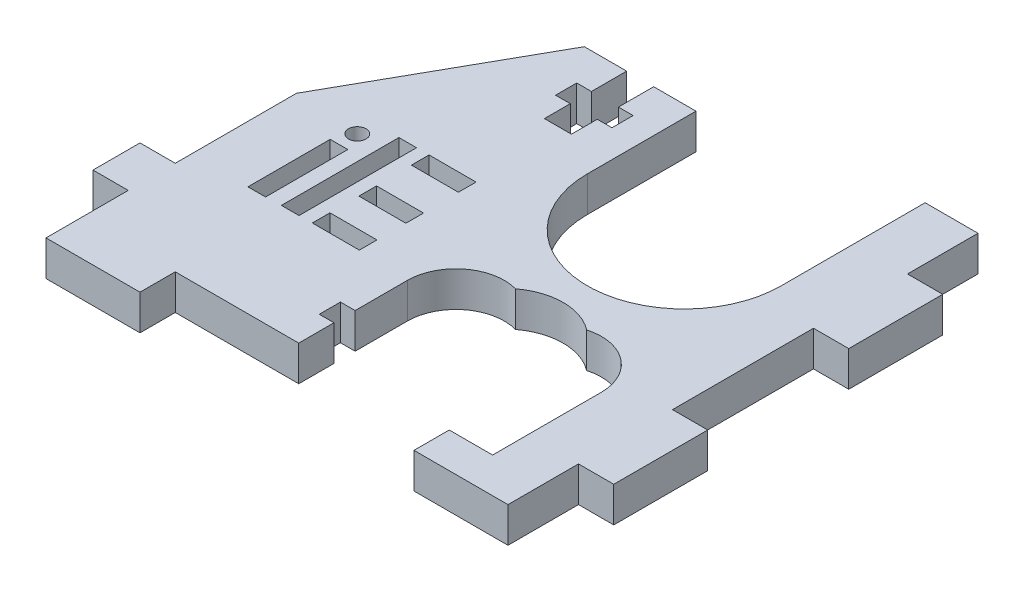
SolidWorks part; units mm, degrees
ref_plane "Front Plane" through (0, 0, 0) normal (0, 0, 1) x (1, 0, 0)
ref_plane "Top Plane" through (0, 0, 0) normal (0, 1, 0) x (1, 0, 0)
ref_plane "Right Plane" through (0, 0, 0) normal (1, 0, 0) x (0, 0, -1)
sketch "Sketch1" plane through (0, 0, 0) normal (0, 1, 0) x (1, 0, 0)
  line L1 (15.25, 17) -> (-15.25, 17)
  line L2 (15.25, 17) -> (15.25, -17)
  line L3 (15.25, -17) -> (-15.25, -17)
  line L4 (-15.25, 17) -> (-15.25, -17)
  line L5 (15.25, 17) -> (-15.25, -17) construction
  line L6 (15.25, -17) -> (-15.25, 17) construction
  point P0 (0, 0)
  dimension "D1" = 30.5
  dimension "D2" = 34
extrude "Boss-Extrude1" add sketch "Sketch1" along normal mid plane 3
sketch "Sketch2" plane through (0, 1.5, 0) normal (0, 1, 0) x (1, 0, 0)
  line L1 (-15.25, 17) -> (-24.07, 1.309)
  line L2 (-55.3828, -17) -> (-15.25, -17)
  line L3 (-15.25, -17) -> (15.25, -17) construction
  line L4 (-15.25, 17) -> (-15.25, -17)
  line L6 (-55.3828, -17) -> (-55.3828, -27.8535) construction
  spline S0 degree 3 poles (-24.07, 1.309) (-25.6121, -1.4345) (-30.226, -1.523) (-46.6978, -11.0884) (-55.3828, -10.3072) (-55.3828, -17) knots 0 0 0 0 0.22113 0.6036 1 1 1 1
  dimension "D2" = 8.82
  dimension "D1" = 18
extrude "Boss-Extrude2" add sketch "Sketch2" against normal up to vertex (3 mm away)
sketch "Sketch3" plane through (0, 1.5, 0) normal (0, 1, 0) x (1, 0, 0)
  line L0 (15.25, -17) -> (15.25, 17) construction
  line L1 (15.25, 14) -> (18.25, 14)
  line L2 (15.25, 14) -> (15.25, 6)
  line L3 (15.25, 6) -> (18.25, 6)
  line L4 (18.25, 14) -> (18.25, 6)
  line L5 (16.75, -6) -> (16.75, 6) construction
  line L6 (15.25, -6) -> (18.25, -6)
  line L7 (15.25, -6) -> (15.25, -14)
  line L8 (15.25, -14) -> (18.25, -14)
  line L9 (18.25, -6) -> (18.25, -14)
  line L10 (0, 0) -> (16.75, 0) construction
  line L11 (-55.3828, -17) -> (15.25, -17) construction
  line L12 (-15.25, 17) -> (-7.25, 17)
  line L13 (-15.25, 17) -> (-15.25, 20)
  line L14 (-15.25, 20) -> (-7.25, 20)
  line L15 (-7.25, 17) -> (-7.25, 20)
  line L16 (15.25, 17) -> (7.25, 17)
  line L17 (15.25, 17) -> (15.25, 20)
  line L18 (15.25, 20) -> (7.25, 20)
  line L19 (7.25, 17) -> (7.25, 20)
  line L20 (-55.3828, -17) -> (-47.3828, -17)
  line L21 (-55.3828, -17) -> (-55.3828, -20)
  line L22 (-55.3828, -20) -> (-47.3828, -20)
  line L23 (-47.3828, -17) -> (-47.3828, -20)
  line L24 (15.25, -17) -> (7.25, -17)
  line L25 (15.25, -17) -> (15.25, -20)
  line L26 (15.25, -20) -> (7.25, -20)
  line L27 (7.25, -17) -> (7.25, -20)
  line L28 (-24.0664, -17) -> (-16.0664, -17)
  line L29 (-24.0664, -17) -> (-24.0664, -20)
  line L30 (-24.0664, -20) -> (-16.0664, -20)
  line L31 (-16.0664, -17) -> (-16.0664, -20)
  line L32 (-47.3828, -18.5) -> (-24.0664, -18.5) construction
  line L33 (-16.0664, -18.5) -> (7.25, -18.5) construction
  dimension "D1" = 3
  dimension "D2" = 8
  dimension "D3" = 12
extrude "Boss-Extrude3" add sketch "Sketch3" against normal up to vertex (3 mm away)
sketch "Sketch4" plane through (0, 1.5, 0) normal (0, 1, 0) x (1, 0, 0)
  line L0 (7.25, 17) -> (-7.25, 17) construction
  line L1 (-1.15, 17) -> (1.15, 17)
  line L2 (-1.15, 17) -> (-1.15, 14)
  line L3 (-1.15, 10) -> (1.15, 10)
  line L4 (1.15, 17) -> (1.15, 14)
  line L5 (0, 0) -> (0, 10) construction
  line L6 (1.15, 12.2) -> (2.4, 12.2)
  line L7 (-2.4, 14) -> (-1.15, 14)
  line L8 (-2.4, 14) -> (-2.4, 12.2)
  line L9 (-2.4, 12.2) -> (-1.15, 12.2)
  line L10 (2.4, 14) -> (2.4, 12.2)
  line L11 (-1.15, 12.2) -> (-1.15, 10)
  line L12 (1.15, 12.2) -> (1.15, 10)
  line L13 (1.15, 14) -> (2.4, 14)
  line L14 (-2.0082, -12.2) -> (-3.2582, -12.2)
  line L15 (-5.5582, -12.2) -> (-6.8082, -12.2)
  line L16 (-3.2582, -17) -> (-5.5582, -17)
  line L17 (-5.5582, -12.2) -> (-5.5582, -10)
  line L18 (-3.2582, -12.2) -> (-3.2582, -10)
  line L19 (-2.0082, -14) -> (-2.0082, -12.2)
  line L20 (-3.2582, -10) -> (-5.5582, -10)
  line L21 (-6.8082, -14) -> (-6.8082, -12.2)
  line L22 (-5.5582, -14) -> (-6.8082, -14)
  line L23 (-3.2582, -17) -> (-3.2582, -14)
  line L24 (-5.5582, -17) -> (-5.5582, -14)
  line L25 (-2.0082, -14) -> (-3.2582, -14)
  line L26 (-33.3246, -12.2) -> (-34.5746, -12.2)
  line L27 (-36.8746, -12.2) -> (-38.1246, -12.2)
  line L28 (-34.5746, -17) -> (-36.8746, -17)
  line L29 (-36.8746, -12.2) -> (-36.8746, -10)
  line L30 (-34.5746, -12.2) -> (-34.5746, -10)
  line L31 (-33.3246, -14) -> (-33.3246, -12.2)
  line L32 (-34.5746, -10) -> (-36.8746, -10)
  line L33 (-38.1246, -14) -> (-38.1246, -12.2)
  line L34 (-36.8746, -14) -> (-38.1246, -14)
  line L35 (-34.5746, -17) -> (-34.5746, -14)
  line L36 (-36.8746, -17) -> (-36.8746, -14)
  line L37 (-33.3246, -14) -> (-34.5746, -14)
  line L38 (-4.4082, -17) -> (-4.4082, -10) construction
  line L39 (-16.0664, -17) -> (7.25, -17) construction
  line L40 (-35.7246, -17) -> (-35.7246, -10) construction
  line L41 (-47.3828, -17) -> (-24.0664, -17) construction
  point P49 (-35.7246, -17)
  dimension "D1" = 2.3
  dimension "D2" = 7
  dimension "D3" = 4.8
  dimension "D4" = 3
  dimension "D5" = 1.8
  dimension "D6" = 2.3
  dimension "D7" = 7
  dimension "D8" = 4.8
  dimension "D9" = 1.8
  dimension "D10" = 2.3
  dimension "D11" = 7
  dimension "D12" = 4.8
  dimension "D13" = 1.8
  dimension "D14" = 3
  dimension "D15" = 3
extrude "Cut-Extrude1" cut sketch "Sketch4" against normal through all contours L25 L19 L14 L18 L20 L17 L15 L21 L22 L24 L23 M17 | L37 L31 L26 L30 L32 L29 L27 L33 L34 L36 L35 M13
sketch "Sketch5" plane through (0, 1.5, 0) normal (0, 1, 0) x (1, 0, 0)
  line L0 (10.75, 20) -> (10.75, 7.75)
  line L1 (15.25, 20) -> (7.25, 20) construction
  line L3 (-5.75, 20) -> (-5.75, 7.75)
  line L10 (-5.75, 20) -> (10.75, 20)
  line L11 (15.25, 14) -> (15.25, 20) construction
  arc A0 (-5.75, 7.75) -> (10.75, 7.75) centre (2.5, 7.75) ccw
  dimension "D1" = 20.5
  dimension "D2" = 4.5
  dimension "D3" = 16.5
extrude "Cut-Extrude2" cut sketch "Sketch5" against normal through all
sketch "Sketch6" plane through (0, 1.5, 0) normal (0, 1, 0) x (1, 0, 0)
  line L1 (-7.25, 17) -> (-15.25, 17)
  line L2 (-7.25, 17) -> (-7.25, 20)
  line L3 (-7.25, 20) -> (-15.25, 20)
  line L4 (-15.25, 17) -> (-15.25, 20)
extrude "Cut-Extrude3" cut sketch "Sketch6" against normal through all
sketch "Sketch7" plane through (0, 1.5, 0) normal (0, 1, 0) x (1, 0, 0)
  line L0 (-5.75, 17) -> (-15.25, 17) construction
  line L1 (-11.65, 17) -> (-9.35, 17)
  line L2 (-11.65, 17) -> (-11.65, 14)
  line L3 (-11.65, 10) -> (-9.35, 10)
  line L4 (-9.35, 17) -> (-9.35, 14)
  line L5 (-11.65, 12.2) -> (-11.65, 10)
  line L6 (-12.9, 14) -> (-11.65, 14)
  line L7 (-12.9, 14) -> (-12.9, 12.2)
  line L8 (-12.9, 12.2) -> (-11.65, 12.2)
  line L9 (-8.1, 14) -> (-8.1, 12.2)
  line L10 (-9.35, 12.2) -> (-8.1, 12.2)
  line L11 (-9.35, 12.2) -> (-9.35, 10)
  line L12 (-9.35, 14) -> (-8.1, 14)
  line L13 (-10.5, 10) -> (-10.5, 17) construction
  point P16 (-10.5, 17)
  dimension "D1" = 2.3
  dimension "D2" = 1.8
  dimension "D3" = 4.8
  dimension "D4" = 3
  dimension "D5" = 7
extrude "Cut-Extrude4" cut sketch "Sketch7" against normal through all
sketch "Sketch8" plane through (0, 1.5, 0) normal (0, 1, 0) x (1, 0, 0)
  line L0 (-24.0664, -17) -> (-24.0664, 1.3154)
  line L2 (-15.25, 17) -> (-24.07, 1.309) construction
  line L61 (10.75, 20) -> (10.75, 7.75)
  line L62 (-5.75, 7.75) -> (-5.75, 17)
  line L63 (-12.9, 14) -> (-11.65, 14)
  line L64 (-11.65, 14) -> (-11.65, 17)
  line L65 (-11.65, 17) -> (-15.25, 17)
  line L66 (-15.25, 17) -> (-24.07, 1.309)
  line L67 (-55.3828, -17) -> (-55.3828, -20)
  line L68 (-55.3828, -20) -> (-47.3828, -20)
  line L69 (-47.3828, -20) -> (-47.3828, -17)
  line L70 (-47.3828, -17) -> (-36.8746, -17)
  line L71 (-36.8746, -17) -> (-36.8746, -14)
  line L72 (-36.8746, -14) -> (-38.1246, -14)
  line L73 (-38.1246, -14) -> (-38.1246, -12.2)
  line L74 (-38.1246, -12.2) -> (-36.8746, -12.2)
  line L75 (-36.8746, -12.2) -> (-36.8746, -10)
  line L76 (-36.8746, -10) -> (-34.5746, -10)
  line L77 (-34.5746, -10) -> (-34.5746, -12.2)
  line L78 (-34.5746, -12.2) -> (-33.3246, -12.2)
  line L79 (-33.3246, -12.2) -> (-33.3246, -14)
  line L80 (-33.3246, -14) -> (-34.5746, -14)
  line L81 (-34.5746, -14) -> (-34.5746, -17)
  line L82 (-34.5746, -17) -> (-24.0664, -17)
  line L83 (-24.0664, -17) -> (-24.0664, -20)
  line L84 (-24.0664, -20) -> (-16.0664, -20)
  line L85 (-16.0664, -20) -> (-16.0664, -17)
  line L86 (-16.0664, -17) -> (-5.5582, -17)
  line L87 (-5.5582, -17) -> (-5.5582, -14)
  line L88 (-5.5582, -14) -> (-6.8082, -14)
  line L89 (-6.8082, -14) -> (-6.8082, -12.2)
  line L90 (-6.8082, -12.2) -> (-5.5582, -12.2)
  line L91 (-5.5582, -12.2) -> (-5.5582, -10)
  line L92 (-5.5582, -10) -> (-3.2582, -10)
  line L93 (-3.2582, -10) -> (-3.2582, -12.2)
  line L94 (-3.2582, -12.2) -> (-2.0082, -12.2)
  line L95 (-2.0082, -12.2) -> (-2.0082, -14)
  line L96 (-2.0082, -14) -> (-3.2582, -14)
  line L97 (-3.2582, -14) -> (-3.2582, -17)
  line L98 (-3.2582, -17) -> (7.25, -17)
  line L99 (7.25, -17) -> (7.25, -20)
  line L100 (7.25, -20) -> (15.25, -20)
  line L101 (15.25, -20) -> (15.25, -14)
  line L102 (15.25, -14) -> (18.25, -14)
  line L103 (18.25, -14) -> (18.25, -6)
  line L104 (18.25, -6) -> (15.25, -6)
  line L105 (15.25, -6) -> (15.25, 6)
  line L106 (15.25, 6) -> (18.25, 6)
  line L107 (18.25, 6) -> (18.25, 14)
  line L108 (18.25, 14) -> (15.25, 14)
  line L109 (15.25, 14) -> (15.25, 20)
  line L110 (15.25, 20) -> (10.75, 20)
  line L113 (-5.75, 17) -> (-9.35, 17)
  line L114 (-9.35, 17) -> (-9.35, 14)
  line L115 (-9.35, 14) -> (-8.1, 14)
  line L116 (-8.1, 14) -> (-8.1, 12.2)
  line L117 (-8.1, 12.2) -> (-9.35, 12.2)
  line L118 (-9.35, 12.2) -> (-9.35, 10)
  line L119 (-9.35, 10) -> (-11.65, 10)
  line L120 (-11.65, 10) -> (-11.65, 12.2)
  line L121 (-11.65, 12.2) -> (-12.9, 12.2)
  line L122 (-12.9, 12.2) -> (-12.9, 14)
  line L126 (-24.0664, 1.3154) -> (-24.07, 1.309)
  line L127 (-55.3828, -17) -> (-55.3828, -20)
  line L128 (-55.3828, -20) -> (-47.3828, -20)
  line L129 (-47.3828, -20) -> (-47.3828, -17)
  line L130 (-47.3828, -17) -> (-36.8746, -17)
  line L131 (-36.8746, -17) -> (-36.8746, -14)
  line L132 (-36.8746, -14) -> (-38.1246, -14)
  line L133 (-38.1246, -14) -> (-38.1246, -12.2)
  line L134 (-38.1246, -12.2) -> (-36.8746, -12.2)
  line L135 (-36.8746, -12.2) -> (-36.8746, -10)
  line L136 (-36.8746, -10) -> (-34.5746, -10)
  line L137 (-34.5746, -10) -> (-34.5746, -12.2)
  line L138 (-34.5746, -12.2) -> (-33.3246, -12.2)
  line L139 (-33.3246, -12.2) -> (-33.3246, -14)
  line L140 (-33.3246, -14) -> (-34.5746, -14)
  line L141 (-34.5746, -14) -> (-34.5746, -17)
  line L142 (-34.5746, -17) -> (-24.0664, -17)
  arc A1 (-5.75, 7.75) -> (10.75, 7.75) centre (2.5, 7.75) ccw
  spline S1 degree 3 poles (224.7586, 1985.7153) (-40.4807, -43.8615) (-2.9101, 14.3397) (-79.7572, -30.2865) (-72.6227, 48.3771) (718.9285, -1860.9983) knots -1.65834 -1.65834 -1.65834 -1.65834 0.22113 0.6036 3.007027 3.007027 3.007027 3.007027 only from (-24.07, 1.309) to (-55.3828, -17)
  spline S2 degree 3 poles (-24.07, 1.309) (-25.6121, -1.4345) (-30.226, -1.523) (-46.6978, -11.0884) (-55.3828, -10.3072) (-55.3828, -17) knots 0 0 0 0 0.22113 0.6036 1 1 1 1
  dimension "D1" = 0
extrude "Cut-Extrude6" cut sketch "Sketch8" against normal through all
sketch "Sketch9" plane through (0, 1.5, 0) normal (0, 1, 0) x (1, 0, 0)
  line L0 (-24.0664, 1.3154) -> (-24.0664, -20) construction
  line L1 (-24.0664, -9) -> (-27.0664, -9)
  line L2 (-24.0664, -9) -> (-24.0664, -13)
  line L3 (-24.0664, -13) -> (-27.0664, -13)
  line L4 (-27.0664, -9) -> (-27.0664, -13)
  line L5 (-24.0664, -9) -> (-27.0664, -9) construction
  line L6 (-24.0664, -13) -> (-27.0664, -13) construction
  line L7 (-27.0664, -13) -> (-27.0664, -9) construction
extrude "Cut-Extrude8" cut sketch "Sketch14" against normal blind 10
sketch "Sketch14" plane through (0, 1.5, 0) normal (0, 1, 0) x (1, 0, 0)
  line L0 (-5.5582, -17) -> (10.9418, -17)
  line L2 (-5.5582, -17) -> (-5.5582, -7.75)
  line L5 (10.9418, -17) -> (10.9418, -7.75)
  line L6 (10.9418, -7.75) -> (-5.5582, -7.75)
sketch "Sketch16" plane through (0, 1.5, 0) normal (0, 1, 0) x (1, 0, 0)
  line L0 (2.6918, -7.75) -> (10.9418, -7.75) construction
  line L1 (-5.5582, -7.75) -> (2.6918, -7.75) construction
  circle A1 centre (-1.4332, -7.75) radius 4.125
  circle A2 centre (6.8168, -7.75) radius 4.125
extrude "Cut-Extrude10" cut sketch "Sketch16" against normal blind 10 contours A1 M3 | A2 M3
sketch "Sketch18" plane through (0, 1.5, 0) normal (0, 1, 0) x (1, 0, 0)
  line L0 (-5.5582, -7.75) -> (10.9418, -7.75) construction
  arc A0 (10.9418, -7.75) -> (2.6918, -7.75) centre (6.8168, -7.75) ccw construction
  circle A1 centre (2.6918, -7.75) radius 5
extrude "Cut-Extrude11" cut sketch "Sketch18" against normal blind 10
sketch "Sketch19" plane through (0, 1.5, 0) normal (0, 1, 0) x (1, 0, 0)
  line L0 (-13.8316, -2.1058) -> (-9.8316, -2.1058)
  line L1 (-16.4447, 2.4128) -> (-14.9447, 2.4128)
  line L2 (-16.4447, 2.4128) -> (-16.4447, -7.5872)
  line L3 (-16.4447, -7.5872) -> (-14.9447, -7.5872)
  line L4 (-14.9447, 2.4128) -> (-14.9447, -7.5872)
  line L5 (-13.8316, -2.1058) -> (-13.8316, -3.6058)
  line L6 (-13.8316, -3.6058) -> (-9.8316, -3.6058)
  line L7 (-13.8813, 2.4128) -> (-9.8813, 2.4128)
  line L8 (-13.8813, 2.4128) -> (-13.8813, 0.9128)
  line L9 (-13.8813, 0.9128) -> (-9.8813, 0.9128)
  line L10 (-9.8813, 2.4128) -> (-9.8813, 0.9128)
  line L11 (-9.8316, -2.1058) -> (-9.8316, -3.6058)
  line L12 (-13.8316, -6.0684) -> (-9.8316, -6.0684)
  line L13 (-13.8316, -6.0684) -> (-13.8316, -7.5684)
  line L14 (-13.8316, -7.5684) -> (-9.8316, -7.5684)
  line L15 (-9.8316, -6.0684) -> (-9.8316, -7.5684)
  line L16 (-14.9447, 2.4128) -> (-14.9447, -7.5872) construction
  line L17 (-19.2378, -0.6438) -> (-17.7378, -0.6438)
  line L18 (-19.2378, -0.6438) -> (-19.2378, -7.6438)
  line L19 (-19.2378, -7.6438) -> (-17.7378, -7.6438)
  line L20 (-17.7378, -0.6438) -> (-17.7378, -7.6438)
  circle A0 centre (-18.4878, 0.9128) radius 0.75
extrude "Cut-Extrude12" cut sketch "Sketch19" against normal blind 10
extrude "Boss-Extrude4" add sketch "Sketch9" against normal up to vertex (3 mm away)
